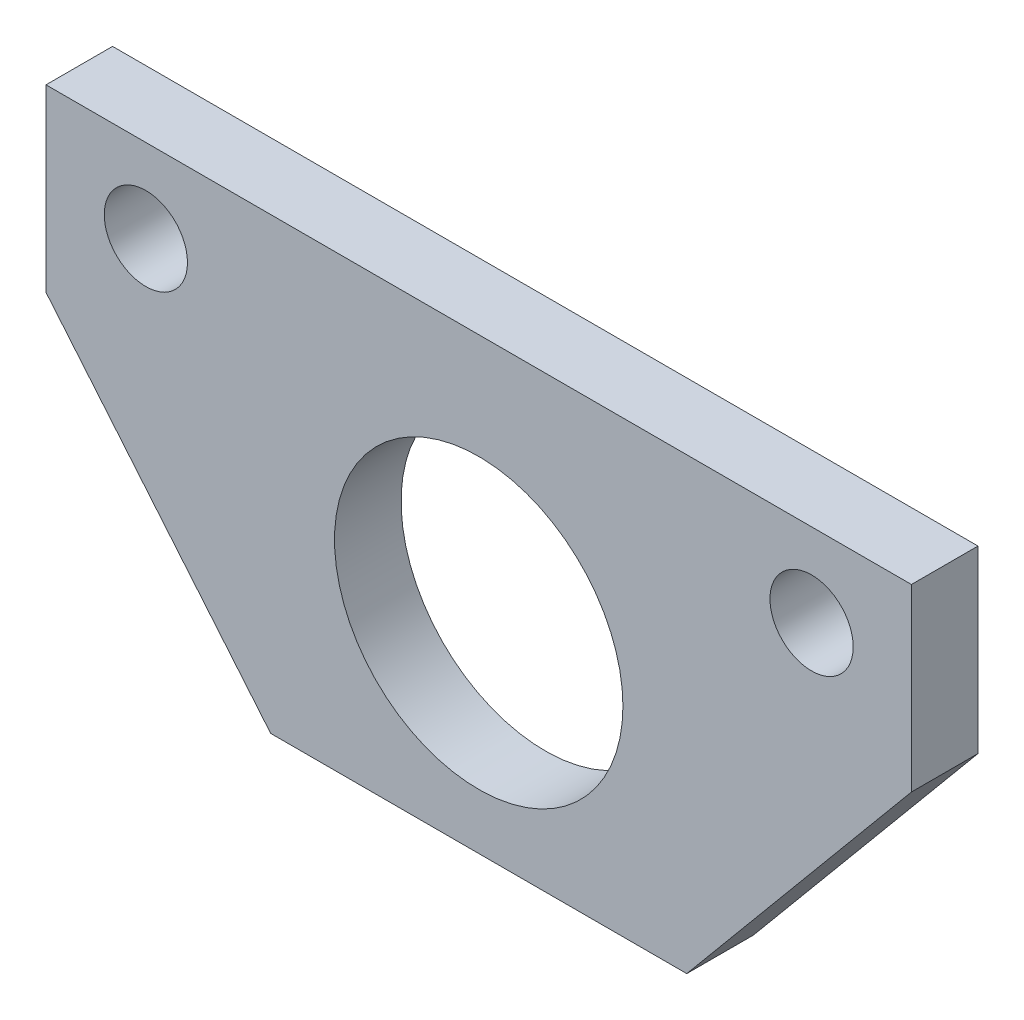
SolidWorks part; units mm, degrees
ref_plane "Front Plane" through (0, 0, 0) normal (0, 0, 1) x (1, 0, 0)
ref_plane "Top Plane" through (0, 0, 0) normal (0, 1, 0) x (1, 0, 0)
ref_plane "Right Plane" through (0, 0, 0) normal (1, 0, 0) x (0, 0, -1)
sketch "Sketch1" plane through (0, 0, 0) normal (0, 0, 1) x (1, 0, 0)
  line L0 (-44.45, 38.1) -> (44.45, 38.1)
  line L5 (44.45, 38.1) -> (12.7, 0)
  line L6 (-44.45, 38.1) -> (-12.7, 0)
  line L11 (-12.7, 0) -> (12.7, 0)
  point P4 (0, 38.1)
  point P6 (0, 0)
  dimension "D1" = 25.4
  dimension "D2" = 88.9
  dimension "D3" = 38.1
extrude "Boss-Extrude1" add sketch "Sketch1" along normal blind 5.08
sketch "Sketch3" plane through (0, 0, 5.08) normal (0, 0, 1) x (1, 0, 0)
  line L0 (-25.4, 31.75) -> (25.4, 31.75) construction
  line L1 (-33.02, 24.384) -> (-33.02, 38.1)
  line L2 (-44.45, 38.1) -> (-12.7, 0) construction
  line L3 (-44.45, 38.1) -> (44.45, 38.1) construction
  line L4 (-33.02, 38.1) -> (-44.45, 38.1)
  line L5 (-44.45, 38.1) -> (-33.02, 24.384)
  line L6 (33.02, 38.1) -> (33.02, 24.384)
  line L7 (44.45, 38.1) -> (12.7, 0) construction
  line L8 (33.02, 24.384) -> (44.45, 38.1)
  line L9 (44.45, 38.1) -> (33.02, 38.1)
  circle A0 centre (0, 19.05) radius 11.0046
  circle A1 centre (-25.4, 31.75) radius 3.175
  circle A2 centre (25.4, 31.75) radius 3.175
  point P7 (0, 31.75)
  dimension "D1" = 22.0091
  dimension "D3" = 6.35
  dimension "D2" = 19.05
  dimension "D4" = 12.7
  dimension "D5" = 50.8
  dimension "D6" = 7.62
extrude "Cut-Extrude2" cut sketch "Sketch3" against normal blind 5.08
sketch "Sketch4" plane through (0, 0, 5.08) normal (0, 0, 1) x (1, 0, 0)
  line L0 (-12.7, 0) -> (12.7, 0) construction
  line L1 (-19.05, 0) -> (19.05, 0)
  line L2 (-19.05, 0) -> (-19.05, 3.81)
  line L3 (-19.05, 3.81) -> (19.05, 3.81)
  line L4 (19.05, 0) -> (19.05, 3.81)
  point P4 (0, 3.81)
  dimension "D1" = 38.1
  dimension "D2" = 3.81
extrude "Cut-Extrude3" cut sketch "Sketch4" against normal through all
